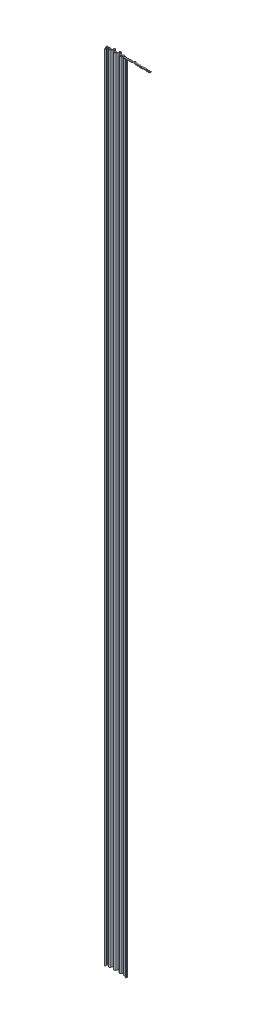
SolidWorks part; units mm, degrees
material "6463-T6"
ref_plane "Front Plane" through (0, 0, 0) normal (0, 0, 1) x (1, 0, 0)
ref_plane "Top Plane" through (0, 0, 0) normal (0, 1, 0) x (1, 0, 0)
ref_plane "Right Plane" through (0, 0, 0) normal (1, 0, 0) x (0, 0, -1)
sketch "Sketch1" plane through (0, 0, 0) normal (0, 1, 0) x (1, 0, 0)
  line L0 (0, 6.35) -> (101.6, 6.35) construction
  line L1 (0, 0) -> (101.6, 0)
  line L2 (0, 0) -> (0, 25.4)
  line L3 (0, 25.4) -> (101.6, 25.4)
  line L5 (0, 6.35) -> (101.6, 6.35) construction
  line L6 (0, 17.3278) -> (101.6, 17.3278) construction
  line L7 (50.8, 25.4) -> (50.8, 0) construction
  line L8 (16.917, 25.4) -> (16.917, 0) construction
  line L9 (85.9039, 25.4) -> (85.9039, 0) construction
  line L11 (41.1101, 25.4) -> (41.1101, 0) construction
  line L12 (66.7907, 25.4) -> (66.7907, 0) construction
  line L14 (101.6, 12.7) -> (203.2, 12.7) construction
  line L15 (101.6, 0) -> (203.2, 0)
  line L16 (101.6, 0) -> (101.6, 25.4)
  line L17 (101.6, 25.4) -> (203.2, 25.4)
  line L18 (203.2, 0) -> (203.2, 25.4)
  line L19 (101.6, 6.35) -> (203.2, 6.35) construction
  line L20 (101.6, 17.3278) -> (203.2, 17.3278) construction
  line L21 (152.4, 25.4) -> (152.4, 0) construction
  line L22 (138.221, 25.4) -> (138.221, 0) construction
  line L23 (187.4631, 25.4) -> (187.4631, 0) construction
  line L24 (118.3926, 25.4) -> (118.3926, 0) construction
  line L25 (154.6686, 25.4) -> (154.6686, 0) construction
  line L26 (170.2261, 25.4) -> (170.2261, 0) construction
  line L28 (0, 12.7) -> (101.6, 12.7) construction
  line L29 (210.274, 12.7) -> (196.1252, 12.7) construction
  line L30 (187.4027, 14.6866) -> (178.5609, 14.6866) construction
  line L31 (171.3703, 12.7) -> (156.7917, 12.7) construction
  line L32 (138.7785, 17.3278) -> (120.837, 17.3278) construction
  line L33 (61.0008, 25.4) -> (33.1464, 25.4) construction
  line L34 (104.3408, 12.7) -> (84.6997, 12.7) construction
  line L35 (9.9511, 12.7) -> (-9.952, 12.7) construction
  line L36 (3.453, 8.5498) -> (5.7941, 13.5702)
  line L37 (20.37, 8.5498) -> (26.2604, 21.1817)
  line L38 (44.5632, 8.5498) -> (51.8653, 24.2093)
  line L39 (70.2437, 8.5498) -> (74.3307, 17.3144)
  line L40 (89.3569, 8.5498) -> (91.4859, 13.1154)
  line L41 (105.053, 8.5498) -> (107.3982, 13.5791)
  line L42 (121.8456, 8.5498) -> (125.9374, 17.3246)
  line L43 (141.674, 8.5498) -> (144.2206, 14.0111)
  line L44 (158.1216, 8.5498) -> (160.0615, 12.7099)
  line L45 (173.6792, 8.5498) -> (176.324, 14.2217)
  line L46 (190.9161, 8.5498) -> (193.0427, 13.1103)
  line L47 (13.464, 8.5498) -> (10.4565, 14.9995)
  line L48 (37.6571, 8.5498) -> (30.9624, 22.9067)
  line L49 (63.3377, 8.5498) -> (56.6172, 22.9619)
  line L50 (82.4508, 8.5498) -> (79.0267, 15.893)
  line L51 (98.147, 8.5498) -> (96.1989, 12.7275)
  line L52 (114.9396, 8.5498) -> (112.0907, 14.6592)
  line L53 (134.7679, 8.5498) -> (130.7643, 17.1355)
  line L54 (151.2155, 8.5498) -> (148.9506, 13.407)
  line L55 (166.7731, 8.5498) -> (164.7918, 12.7988)
  line L56 (184.01, 8.5498) -> (181.1522, 14.6784)
  line L57 (199.747, 8.5498) -> (197.7713, 12.7866)
  circle A0 centre (0, 10.16) radius 3.81
  circle A1 centre (101.6, 10.16) radius 3.81
  circle A2 centre (203.2, 10.16) radius 3.81
  circle A3 centre (16.917, 10.16) radius 3.81
  circle A4 centre (41.1101, 10.16) radius 3.81
  circle A5 centre (85.9039, 10.16) radius 3.81
  circle A6 centre (66.7907, 10.16) radius 3.81
  circle A7 centre (118.3926, 10.16) radius 3.81
  circle A8 centre (138.221, 10.16) radius 3.81
  circle A9 centre (154.6686, 10.16) radius 3.81
  circle A10 centre (170.2261, 10.16) radius 3.81
  circle A11 centre (187.4631, 10.16) radius 3.81
  circle A12 centre (8.4585, 10.4217) radius 3.7454
  circle A13 centre (29.0136, 18.2235) radius 3.7454
  circle A14 centre (53.9504, 19.8184) radius 3.7454
  circle A15 centre (76.3473, 12.7765) radius 3.7454
  circle A16 centre (93.7519, 9.1126) radius 3.7454
  circle A17 centre (109.9963, 10.2883) radius 3.7454
  circle A18 centre (128.3068, 13.5434) radius 3.7454
  circle A19 centre (146.4448, 9.9184) radius 3.7454
  circle A20 centre (162.4474, 8.964) radius 3.7454
  circle A21 centre (178.8446, 10.7647) radius 3.7454
  circle A22 centre (195.3315, 9.1563) radius 3.7454
  spline S0 degree 3 poles (0, 12.7) (9.8081, 12.7) (31.7818, 25.9219) (56.1889, 25.0612) (82.5909, 12.5082) (110.3234, 12.739) (117.9598, 17.6185) (139.5004, 17.014) (135.4155, 13.8526) (167.1855, 12.2761) (177.8205, 14.8691) (190.6404, 14.4038) (188.7233, 12.7) (203.2, 12.7) knots 0 0 0 0 0.151649 0.189034 0.35331 0.391068 0.528853 0.570469 0.765612 0.797753 0.859739 0.880738 1 1 1 1
  dimension "D11" = 65
  dimension "D7" = 101.6
  dimension "D9" = 7.62
  dimension "D3" = 7.4908
  dimension "D1" = 101.6
  dimension "D2" = 25.4
  dimension "D4" = 6.35
  dimension "D5" = 101.6
  dimension "D6" = 25.4
  dimension "D8" = 6.35
  dimension "D10" = 65
  dimension "D12" = 5.7941
  dimension "D13" = 8.4585
  dimension "D14" = 26.2604
  dimension "D15" = 44.5632
extrude "Boss-Extrude1" add sketch "Sketch1" along normal blind 2.54 contours S0 L2 A0 | A12 | A3 | A13 | A4 | A14 | A6 | A15 | A5 | A16 | S0 A1 L16 | S0 L16 A1 | A1 S0 L16 | L16 S0 A1 | A17 | A7 | A18 | A8 | A19 | S0 A9 | A9 S0 | A20 | S0 A10 | A21 | A11 | A22 | S0 A2 L18 | A2 S0 L18 | L2 S0 A0
sketch "Sketch3" plane through (0, 0, 0) normal (0, -1, 0) x (1, 0, 0)
  line L0 (4.8342, -7.9058) -> (6.4452, -11.3605)
  line L1 (0, -6.35) -> (0, -13.97)
  line L5 (12.0828, -7.9058) -> (10.4718, -11.3605)
  line L6 (141.674, -8.5498) -> (144.2206, -14.0111) construction
  line L7 (134.7679, -8.5498) -> (130.7643, -17.1355) construction
  line L8 (121.8456, -8.5498) -> (125.9374, -17.3246) construction
  line L9 (114.9396, -8.5498) -> (112.0907, -14.6592) construction
  line L10 (105.053, -8.5498) -> (107.3982, -13.5791) construction
  line L11 (98.147, -8.5498) -> (96.1989, -12.7275) construction
  line L12 (89.3569, -8.5498) -> (91.4859, -13.1154) construction
  line L13 (82.4508, -8.5498) -> (79.0267, -15.893) construction
  line L14 (70.2437, -8.5498) -> (74.3307, -17.3144) construction
  line L15 (63.3377, -8.5498) -> (56.6172, -22.9619) construction
  line L16 (44.5632, -8.5498) -> (51.8653, -24.2093) construction
  line L17 (37.6571, -8.5498) -> (30.9624, -22.9067) construction
  line L18 (20.37, -8.5498) -> (26.2604, -21.1817) construction
  line L19 (13.464, -8.5498) -> (10.4565, -14.9995) construction
  line L20 (3.453, -8.5498) -> (5.7941, -13.5702) construction
  line L21 (141.674, -8.5498) -> (143.0503, -11.5012)
  line L22 (134.7679, -8.5498) -> (131.7013, -15.1263)
  line L23 (121.8456, -8.5498) -> (124.9123, -15.1263)
  line L24 (114.9396, -8.5498) -> (113.3908, -11.8712)
  line L25 (105.053, -8.5498) -> (106.6018, -11.8712)
  line L26 (98.147, -8.5498) -> (97.1464, -10.6955)
  line L27 (89.3569, -8.5498) -> (90.3574, -10.6955)
  line L28 (82.4508, -8.5498) -> (79.7418, -14.3594)
  line L29 (70.2437, -8.5498) -> (72.9528, -14.3594)
  line L30 (63.3377, -8.5498) -> (57.3449, -21.4013)
  line L31 (44.5632, -8.5498) -> (50.5559, -21.4013)
  line L32 (37.6571, -8.5498) -> (32.4081, -19.8064)
  line L33 (20.37, -8.5498) -> (25.6191, -19.8064)
  line L34 (13.464, -8.5498) -> (11.853, -12.0046)
  line L35 (3.453, -8.5498) -> (5.064, -12.0046)
  line L36 (199.747, -8.5498) -> (197.7713, -12.7866) construction
  line L37 (190.9161, -8.5498) -> (193.0427, -13.1103) construction
  line L38 (184.01, -8.5498) -> (181.1522, -14.6784) construction
  line L39 (173.6792, -8.5498) -> (176.324, -14.2217) construction
  line L40 (166.7731, -8.5498) -> (164.7918, -12.7988) construction
  line L41 (158.1216, -8.5498) -> (160.0615, -12.7099) construction
  line L42 (151.2155, -8.5498) -> (148.9506, -13.407) construction
  line L43 (199.747, -8.5498) -> (198.726, -10.7392)
  line L44 (190.9161, -8.5498) -> (191.937, -10.7392)
  line L45 (184.01, -8.5498) -> (182.2391, -12.3476)
  line L46 (173.6792, -8.5498) -> (175.4501, -12.3476)
  line L47 (166.7731, -8.5498) -> (165.8419, -10.5469)
  line L48 (158.1216, -8.5498) -> (159.0529, -10.5469)
  line L49 (151.2155, -8.5498) -> (149.8393, -11.5012)
  line L50 (21.7513, -7.9058) -> (27.0003, -19.1623)
  line L51 (36.2759, -7.9058) -> (31.0269, -19.1623)
  line L52 (45.9444, -7.9058) -> (51.9371, -20.7572)
  line L53 (61.9564, -7.9058) -> (55.9637, -20.7572)
  line L54 (71.6249, -7.9058) -> (74.334, -13.7153)
  line L55 (81.0696, -7.9058) -> (78.3606, -13.7153)
  line L56 (90.7381, -7.9058) -> (91.7386, -10.0514)
  line L57 (96.7658, -7.9058) -> (95.7652, -10.0514)
  line L58 (106.4342, -7.9058) -> (107.983, -11.2271)
  line L59 (113.5584, -7.9058) -> (112.0096, -11.2271)
  line L60 (123.2269, -7.9058) -> (126.2935, -14.4822)
  line L61 (133.3867, -7.9058) -> (130.3201, -14.4822)
  line L62 (143.0552, -7.9058) -> (144.4315, -10.8572)
  line L63 (149.8343, -7.9058) -> (148.4581, -10.8572)
  line L64 (159.5028, -7.9058) -> (160.4341, -9.9028)
  line L65 (165.3919, -7.9058) -> (164.4607, -9.9028)
  line L66 (175.0604, -7.9058) -> (176.8313, -11.7035)
  line L67 (182.6288, -7.9058) -> (180.8579, -11.7035)
  line L68 (192.2973, -7.9058) -> (193.3182, -10.0951)
  line L69 (198.3658, -7.9058) -> (197.3448, -10.0951)
  line L70 (0, -6.35) -> (0, -4.826)
  line L71 (203.2, -6.35) -> (203.2, -4.826)
  circle A0 centre (101.6, -10.16) radius 3.81 construction
  arc A1 (0, -13.97) -> (0, -6.35) centre (0, -10.16) ccw
  arc A2 (3.453, -8.5498) -> (0, -6.35) centre (0, -10.16) ccw
  circle A3 centre (8.4585, -10.4217) radius 3.7454
  arc A4 (5.064, -12.0046) -> (11.853, -12.0046) centre (8.4585, -10.4217) ccw
  circle A5 centre (16.917, -10.16) radius 3.81
  arc A6 (20.37, -8.5498) -> (13.464, -8.5498) centre (16.917, -10.16) ccw
  circle A7 centre (29.0136, -18.2235) radius 3.7454
  arc A8 (25.6191, -19.8064) -> (32.4081, -19.8064) centre (29.0136, -18.2235) ccw
  circle A9 centre (93.7519, -9.1126) radius 3.7454 construction
  circle A10 centre (85.9039, -10.16) radius 3.81 construction
  circle A11 centre (76.3473, -12.7765) radius 3.7454 construction
  circle A12 centre (66.7907, -10.16) radius 3.81 construction
  circle A13 centre (53.9504, -19.8184) radius 3.7454 construction
  circle A14 centre (41.1101, -10.16) radius 3.81 construction
  arc A15 (105.053, -8.5498) -> (98.147, -8.5498) centre (101.6, -10.16) ccw
  arc A16 (90.3574, -10.6955) -> (97.1464, -10.6955) centre (93.7519, -9.1126) ccw
  arc A17 (89.3569, -8.5498) -> (82.4508, -8.5498) centre (85.9039, -10.16) ccw
  arc A18 (72.9528, -14.3594) -> (79.7418, -14.3594) centre (76.3473, -12.7765) ccw
  arc A19 (70.2437, -8.5498) -> (63.3377, -8.5498) centre (66.7907, -10.16) ccw
  arc A20 (50.5559, -21.4013) -> (57.3449, -21.4013) centre (53.9504, -19.8184) ccw
  arc A21 (44.5632, -8.5498) -> (37.6571, -8.5498) centre (41.1101, -10.16) ccw
  arc A22 (203.2, -6.35) -> (203.2, -13.97) centre (203.2, -10.16) ccw construction
  circle A23 centre (195.3315, -9.1563) radius 3.7454 construction
  circle A24 centre (187.4631, -10.16) radius 3.81 construction
  circle A25 centre (178.8446, -10.7647) radius 3.7454 construction
  circle A27 centre (162.4474, -8.964) radius 3.7454 construction
  circle A28 centre (154.6686, -10.16) radius 3.81 construction
  circle A29 centre (146.4448, -9.9184) radius 3.7454 construction
  circle A30 centre (138.221, -10.16) radius 3.81 construction
  circle A31 centre (128.3068, -13.5434) radius 3.7454 construction
  circle A32 centre (118.3926, -10.16) radius 3.81 construction
  circle A33 centre (109.9963, -10.2883) radius 3.7454 construction
  arc A34 (203.2, -6.35) -> (199.747, -8.5498) centre (203.2, -10.16) ccw
  arc A35 (191.937, -10.7392) -> (198.726, -10.7392) centre (195.3315, -9.1563) ccw
  arc A36 (190.9161, -8.5498) -> (184.01, -8.5498) centre (187.4631, -10.16) ccw
  arc A37 (175.4501, -12.3476) -> (182.2391, -12.3476) centre (178.8446, -10.7647) ccw
  arc A39 (159.0529, -10.5469) -> (165.8419, -10.5469) centre (162.4474, -8.964) ccw
  arc A40 (158.1216, -8.5498) -> (151.2155, -8.5498) centre (154.6686, -10.16) ccw
  arc A41 (143.0503, -11.5012) -> (149.8393, -11.5012) centre (146.4448, -9.9184) ccw
  arc A42 (141.674, -8.5498) -> (134.7679, -8.5498) centre (138.221, -10.16) ccw
  arc A43 (124.9123, -15.1263) -> (131.7013, -15.1263) centre (128.3068, -13.5434) ccw
  arc A44 (121.8456, -8.5498) -> (114.9396, -8.5498) centre (118.3926, -10.16) ccw
  arc A45 (106.6018, -11.8712) -> (113.3908, -11.8712) centre (109.9963, -10.2883) ccw
  arc A46 (173.6792, -8.5498) -> (166.7731, -8.5498) centre (170.2261, -10.16) ccw
  circle A47 centre (170.2261, -10.16) radius 3.81 construction
  arc A48 (4.8342, -7.9058) -> (0, -4.826) centre (0, -10.16) ccw
  arc A49 (6.4452, -11.3605) -> (10.4718, -11.3605) centre (8.4585, -10.4217) ccw
  arc A50 (21.7513, -7.9058) -> (12.0828, -7.9058) centre (16.917, -10.16) ccw
  arc A51 (27.0003, -19.1623) -> (31.0269, -19.1623) centre (29.0136, -18.2235) ccw
  arc A52 (45.9444, -7.9058) -> (36.2759, -7.9058) centre (41.1101, -10.16) ccw
  arc A53 (51.9371, -20.7572) -> (55.9637, -20.7572) centre (53.9504, -19.8184) ccw
  arc A54 (71.6249, -7.9058) -> (61.9564, -7.9058) centre (66.7907, -10.16) ccw
  arc A55 (74.334, -13.7153) -> (78.3606, -13.7153) centre (76.3473, -12.7765) ccw
  arc A56 (90.7381, -7.9058) -> (81.0696, -7.9058) centre (85.9039, -10.16) ccw
  arc A57 (91.7386, -10.0514) -> (95.7652, -10.0514) centre (93.7519, -9.1126) ccw
  arc A58 (106.4342, -7.9058) -> (96.7658, -7.9058) centre (101.6, -10.16) ccw
  arc A59 (107.983, -11.2271) -> (112.0096, -11.2271) centre (109.9963, -10.2883) ccw
  arc A60 (123.2269, -7.9058) -> (113.5584, -7.9058) centre (118.3926, -10.16) ccw
  arc A61 (126.2935, -14.4822) -> (130.3201, -14.4822) centre (128.3068, -13.5434) ccw
  arc A62 (143.0552, -7.9058) -> (133.3867, -7.9058) centre (138.221, -10.16) ccw
  arc A63 (144.4315, -10.8572) -> (148.4581, -10.8572) centre (146.4448, -9.9184) ccw
  arc A64 (159.5028, -7.9058) -> (149.8343, -7.9058) centre (154.6686, -10.16) ccw
  arc A65 (160.4341, -9.9028) -> (164.4607, -9.9028) centre (162.4474, -8.964) ccw
  arc A66 (175.0604, -7.9058) -> (165.3919, -7.9058) centre (170.2261, -10.16) ccw
  arc A67 (176.8313, -11.7035) -> (180.8579, -11.7035) centre (178.8446, -10.7647) ccw
  arc A68 (192.2973, -7.9058) -> (182.6288, -7.9058) centre (187.4631, -10.16) ccw
  arc A69 (193.3182, -10.0951) -> (197.3448, -10.0951) centre (195.3315, -9.1563) ccw
  arc A70 (203.2, -4.826) -> (198.3658, -7.9058) centre (203.2, -10.16) ccw
  dimension "D1" = 0
  dimension "D2" = 0
  dimension "D3" = 0
  dimension "D4" = 0
  dimension "D5" = 1.524
extrude "Boss-Extrude2" add sketch "Sketch3" along normal blind 3657.6 separate body
sketch "Sketch4" plane through (0, 0, 0) normal (0, 1, 0) x (1, 0, 0)
  line L0 (0, 4.826) -> (101.5848, 4.826) construction
  line L2 (203.2, 6.35) -> (203.2, 4.826) construction
  line L3 (101.5848, 48.0285) -> (203.2, 48.0285)
  line L4 (101.5848, 48.0285) -> (101.5848, -35.5853)
  line L5 (101.5848, -35.5853) -> (203.2, -35.5853)
  line L6 (203.2, 48.0285) -> (203.2, -35.5853)
  line L7 (101.5848, 6.5006) -> (101.5848, 4.6513) construction
  dimension "D1" = 101.5848
  dimension "D2" = 41.6785
  dimension "D3" = 41.9353
extrude "Cut-Extrude1" cut sketch "Sketch4" along direction (0, -1, 0) on the side against the normal up to surface (3657.6 mm away)
sketch "Sketch5" plane through (0, 0, 0) normal (0, 1, 0) x (1, 0, 0)
  line L0 (0, 5.588) -> (0.3662, 4.5819)
  line L1 (0, 4.826) -> (0, 6.35) construction
  line L2 (0.3662, 4.5819) -> (0, 4.5819)
  line L3 (0, 4.5819) -> (0, 5.588)
  line L4 (101.5848, 5.588) -> (101.5848, 1.5264)
  line L5 (101.5848, 4.826) -> (101.5848, 6.35) construction
  line L6 (101.5848, 1.5264) -> (100.1065, 1.5264)
  line L7 (100.1065, 1.5264) -> (101.5848, 5.588)
  dimension "D1" = 0.762
  dimension "D2" = 20
  dimension "D3" = 0.762
  dimension "D4" = 20
  dimension "D5" = 1.4783
  dimension "D6" = 101.2186
extrude "Cut-Extrude2" cut sketch "Sketch5" against normal through all
sketch "Sketch6" plane through (0, 0, 0) normal (0, 1, 0) x (1, 0, 0)
  line L0 (50.7848, 31.5292) -> (50.7848, -4.9482) construction
  line L1 (0, 5.588) -> (0, 6.35) construction
  line L2 (0.2748, 4.8331) -> (0.3467, 4.6355)
  line L3 (0, 5.588) -> (0.2748, 4.8331) construction
  line L4 (2.794, 4.6355) -> (0.3445, 4.6355)
  line L5 (2.794, 2.2225) -> (1.7691, 2.2225)
  line L6 (1.411, 1.7112) -> (1.6375, 1.089)
  line L7 (100.1585, 1.7112) -> (99.932, 1.089)
  line L8 (98.7755, 2.2225) -> (99.8005, 2.2225)
  line L9 (98.7755, 4.6355) -> (101.2381, 4.6355)
  line L10 (101.3103, 4.8339) -> (101.2381, 4.6355)
  line L12 (101.5848, 5.588) -> (101.3103, 4.8339) construction
  arc A0 (2.794, 2.2225) -> (2.794, 4.6355) centre (2.794, 3.429) ccw
  arc A1 (0.3458, 4.638) -> (0.3445, 4.6355) centre (2.794, 3.429) ccw
  arc A2 (96.7658, 7.9058) -> (101.3103, 4.8339) centre (101.6, 10.16) ccw construction
  arc A3 (3.8725, 6.4919) -> (3.9832, 5.8869) centre (4.1492, 6.2299) ccw
  arc A4 (97.7186, 6.5013) -> (101.3103, 4.8339) centre (101.6, 10.16) ccw
  arc A5 (1.866, 0.861) -> (3.9832, 5.8869) centre (2.794, 3.429) ccw
  arc A6 (1.866, 0.861) -> (1.6375, 1.089) centre (1.9955, 1.2193) cw
  arc A7 (1.411, 1.7112) -> (1.7691, 2.2225) centre (1.7691, 1.8415) cw
  arc A8 (0.2748, 4.8331) -> (4.8342, 7.9058) centre (0, 10.16) ccw construction
  arc A9 (0.2748, 4.8331) -> (3.8725, 6.4919) centre (0, 10.16) ccw
  arc A10 (100.1585, 1.7112) -> (99.8005, 2.2225) centre (99.8005, 1.8415) ccw
  arc A11 (99.7035, 0.861) -> (99.932, 1.089) centre (99.574, 1.2193) ccw
  arc A12 (99.7035, 0.861) -> (97.6047, 5.8957) centre (98.7755, 3.429) cw
  arc A13 (97.6047, 5.8957) -> (97.7186, 6.5013) centre (97.4413, 6.2399) ccw
  arc A15 (98.7755, 2.2225) -> (98.7755, 4.6355) centre (98.7755, 3.429) cw
  dimension "D2" = 2.413
  dimension "D3" = 5.461
  dimension "D6" = 0.381
  dimension "D7" = 0.381
  dimension "D8" = 0.762
  dimension "D1" = 50.7848
  dimension "D4" = 2.794
  dimension "D5" = 2.921
extrude "Boss-Extrude3" add sketch "Sketch6" against normal through all
fillet "Fillet1" radius 0.508 1 edges at (101.2381, -1828.8, -4.6355)
fillet "Fillet2" radius 0.508 1 edges at (0.3467, -1828.8, -4.6355)
